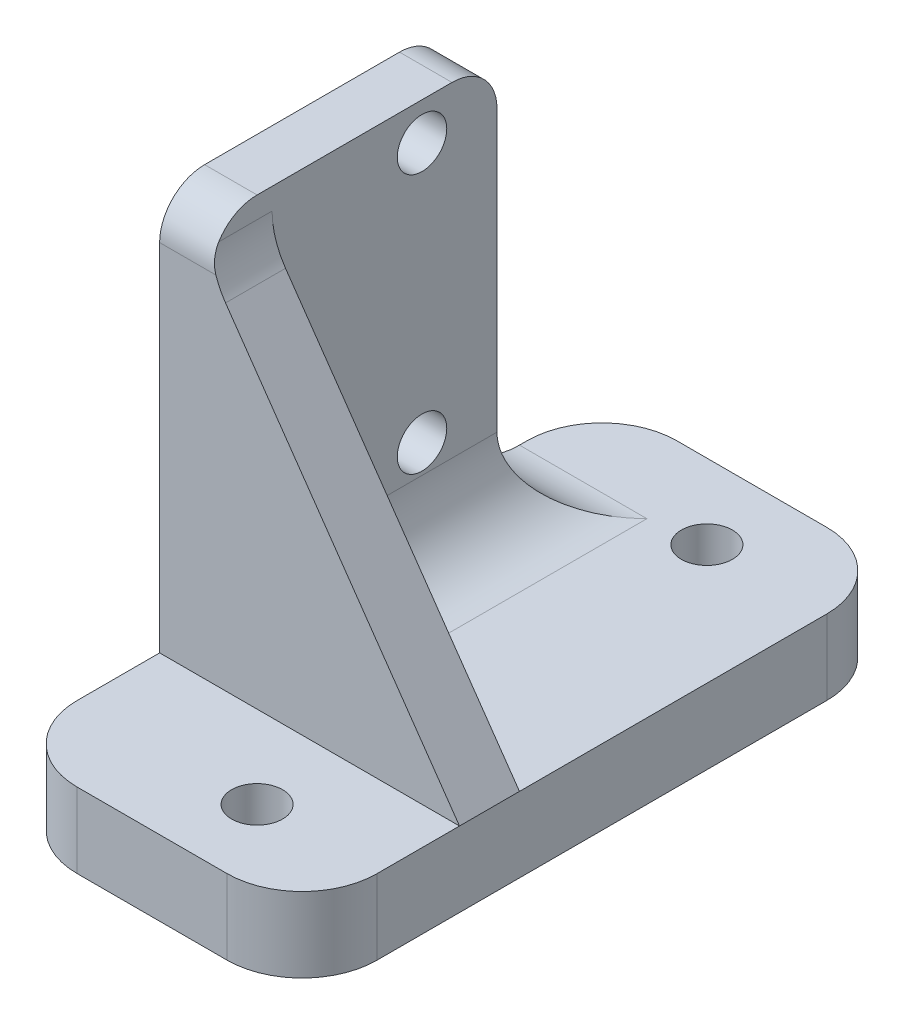
SolidWorks part; units mm, degrees
ref_plane "前视基准面" through (0, 0, 0) normal (0, 0, 1) x (1, 0, 0)
ref_plane "上视基准面" through (0, 0, 0) normal (0, 1, 0) x (1, 0, 0)
ref_plane "右视基准面" through (0, 0, 0) normal (1, 0, 0) x (0, 0, -1)
sketch "草图1" plane through (0, 0, 0) normal (0, 1, 0) x (1, 0, 0)
  line L1 (0, 0) -> (20, 0)
  line L2 (0, 0) -> (0, 40)
  line L3 (0, 40) -> (20, 40)
  line L4 (20, 0) -> (20, 40)
  dimension "D1" = 40
  dimension "D2" = 20
extrude "凸台-拉伸1" add sketch "草图1" along normal blind 5
sketch "草图2" plane through (0, 0, 0) normal (-1, 0, 0) x (0, 0, 1)
  line L0 (-40, 5) -> (0, 5) construction
  line L1 (-29.5, 5) -> (-10.5, 5)
  line L2 (-29.5, 5) -> (-29.5, 31.7)
  line L3 (-29.5, 31.7) -> (-10.5, 31.7)
  line L4 (-10.5, 5) -> (-10.5, 31.7)
  line L5 (-20, 5) -> (-20, 0) construction
  line L6 (-40, 0) -> (0, 0) construction
  dimension "D1" = 19
  dimension "D2" = 26.7
extrude "凸台-拉伸2" add sketch "草图2" against normal blind 3.5
sketch "草图3" plane through (0, 0, 0) normal (-1, 0, 0) x (0, 0, 1)
  line L0 (-29.5, 31.7) -> (-29.5, 5) construction
  line L3 (-10.5, 31.7) -> (-29.5, 31.7) construction
  circle A0 centre (-24.5, 29.2) radius 1.65
  circle A1 centre (-24.5, 11.9) radius 1.65
  dimension "D1" = 3.3
  dimension "D2" = 2.5
  dimension "D3" = 5
  dimension "D4" = 17.3
extrude "切除-拉伸1" cut sketch "草图3" against normal through all
sketch "草图4" plane through (0, 5, 0) normal (0, 1, 0) x (1, 0, 0)
  line L0 (20, 20) -> (13.7526, 20) construction
  line L1 (20, 0) -> (20, 40) construction
  circle A0 centre (12, 35) radius 1.7
  circle A1 centre (12, 5) radius 1.7
  dimension "D1" = 3.4
  dimension "D2" = 30
  dimension "D3" = 8
extrude "切除-拉伸2" cut sketch "草图4" against normal through all
fillet "圆角1" radius 5 4 edges at (0, 2.5, 0) (20, 2.5, -40) (0, 2.5, -40) (20, 2.5, 0)
fillet "圆角2" radius 3 2 edges at (1.75, 31.7, -29.5) (1.75, 31.7, -10.5)
sketch "草图5" plane through (0, 0, -10.5) normal (0, 0, 1) x (1, 0, 0)
  line L0 (3.5, 28.7) -> (20, 5)
rib "筋1" sketch "草图5" sketch "草图5" thickness 4 extrusion direction parallel to sketch draft on no parameters "D1"=4
fillet "圆角3" radius 5 3 edges at (3.5, 5, -22) (3.5, 28.7, -12.5) (1.75, 5, -29.5)
